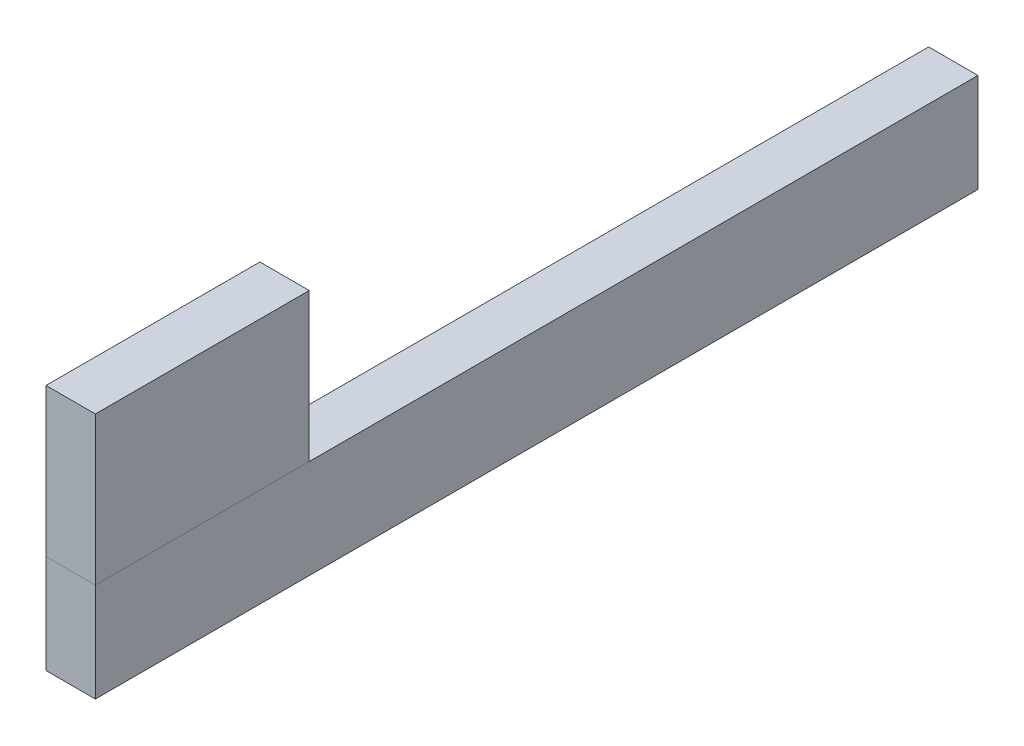
SolidWorks part; units mm, degrees
ref_plane "Front Plane" through (0, 0, 0) normal (0, 0, 1) x (1, 0, 0)
ref_plane "Top Plane" through (0, 0, 0) normal (0, 1, 0) x (1, 0, 0)
ref_plane "Right Plane" through (0, 0, 0) normal (1, 0, 0) x (0, 0, -1)
sketch "Sketch1" plane through (0, 0, 0) normal (0, 0, 1) x (1, 0, 0)
  line L1 (-12.7, 25.4) -> (12.7, 25.4)
  line L2 (-12.7, 25.4) -> (-12.7, -25.4)
  line L3 (-12.7, -25.4) -> (12.7, -25.4)
  line L4 (12.7, 25.4) -> (12.7, -25.4)
  line L5 (-12.7, 25.4) -> (12.7, -25.4) construction
  line L6 (-12.7, -25.4) -> (12.7, 25.4) construction
  point P0 (0, 0)
extrude "Boss-Extrude1" add sketch "Sketch1" along normal blind 454
sketch "Sketch2" plane through (0, 25.4, 0) normal (0, 1, 0) x (1, 0, 0)
  line L0 (12.7, -454) -> (12.7, -344)
  line L1 (12.7, -454) -> (12.7, 0) construction
  line L2 (12.7, -344) -> (-12.7, -344)
  line L3 (-12.7, -454) -> (-12.7, 0) construction
  line L4 (-12.7, -344) -> (-12.7, -454)
  line L5 (-12.7, -454) -> (12.7, -454)
extrude "Boss-Extrude2" add sketch "Sketch2" along normal blind 76.2 separate body
